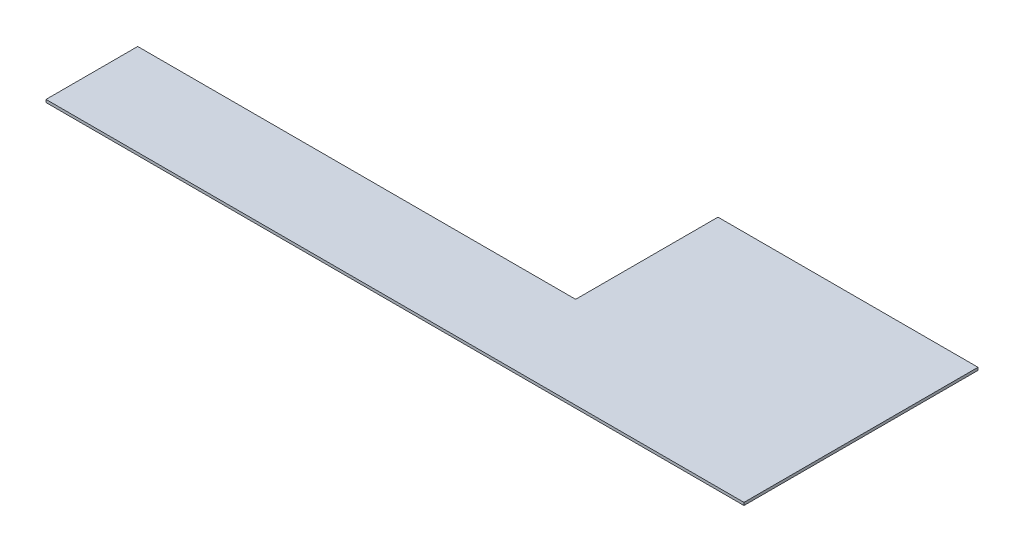
SolidWorks part; units mm, degrees
material "PE High Density"
ref_plane "Front Plane" through (0, 0, 0) normal (0, 0, 1) x (1, 0, 0)
ref_plane "Top Plane" through (0, 0, 0) normal (0, 1, 0) x (1, 0, 0)
ref_plane "Right Plane" through (0, 0, 0) normal (1, 0, 0) x (0, 0, -1)
sketch "Sketch1" plane through (0, 0, 0) normal (0, 1, 0) x (1, 0, 0)
  line L0 (-1016, 0) -> (0, 0)
  line L1 (603.25, -212.725) -> (-1016, -212.725)
  line L2 (603.25, -212.725) -> (603.25, 330.2)
  line L3 (603.25, 330.2) -> (0, 330.2)
  line L4 (-1016, -212.725) -> (-1016, 0)
  line L7 (0, 0) -> (0, 330.2)
  point P0 (0, 0)
  dimension "D1" = 1016
  dimension "D2" = 542.925
  dimension "D3" = 1619.25
  dimension "D4" = 212.725
  dimension "D5" = 603.25
extrude "Boss-Extrude1" add sketch "Sketch1" along normal blind 6.35
